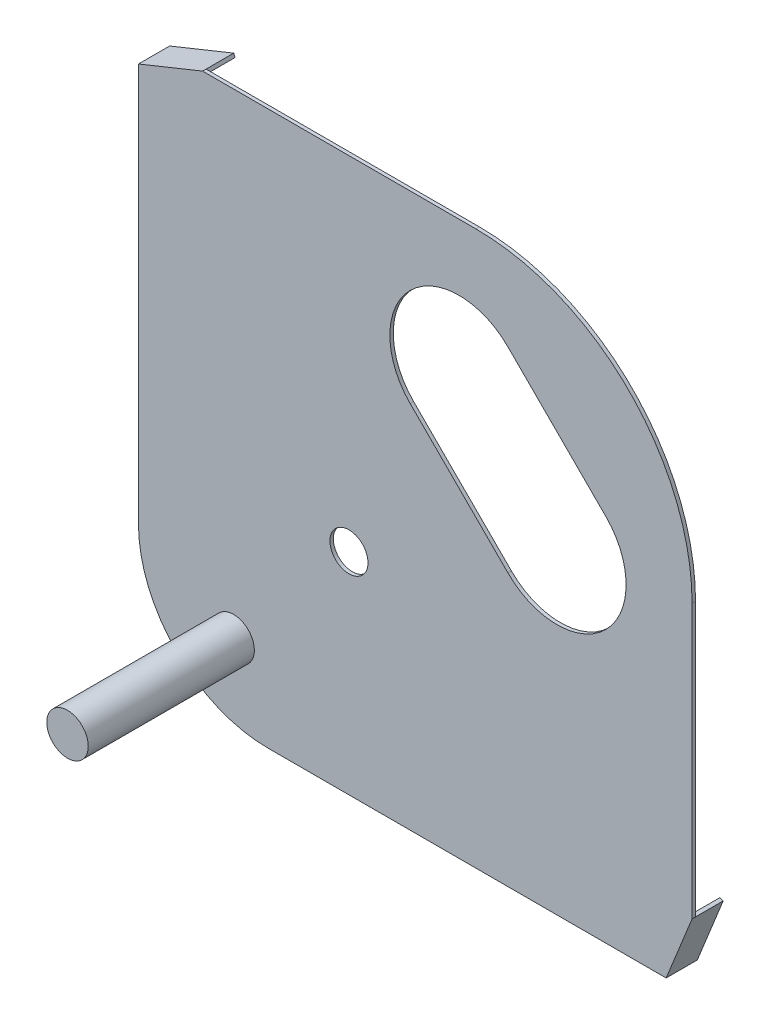
SolidWorks part; units mm, degrees
material "Nickel"
ref_plane "Front Plane" through (0, 0, 0) normal (0, 0, 1) x (1, 0, 0)
ref_plane "Top Plane" through (0, 0, 0) normal (0, 1, 0) x (1, 0, 0)
ref_plane "Right Plane" through (0, 0, 0) normal (1, 0, 0) x (0, 0, -1)
sketch "Sketch1" plane through (0, 0, 0) normal (0, 0, 1) x (1, 0, 0)
  line L0 (0, -9.525) -> (29.212, -9.525)
  line L1 (-9.525, 0) -> (-9.525, 29.212)
  line L2 (-4.8149, 31.115) -> (15.24, 31.115)
  line L3 (31.115, 15.24) -> (31.115, -4.8149)
  line L4 (31.115, -4.8149) -> (29.212, -9.525)
  line L5 (-9.525, 29.212) -> (-4.8149, 31.115)
  arc A0 (-9.525, 0) -> (0, -9.525) centre (0, 0) ccw
  arc A1 (31.115, 15.24) -> (15.24, 31.115) centre (15.24, 15.24) ccw
  dimension "D1" = 19.05
  dimension "D2" = 5.08
  dimension "D4" = 31.75
  dimension "D3" = 40.64
  dimension "D5" = 40.64
  dimension "D6" = 22
  dimension "D7" = 5.08
  dimension "D8" = 22
extrude "Boss-Extrude1" add sketch "Sketch1" against normal blind 0.254
sketch "Sketch2" plane through (0, 0, 0) normal (0, 0, 1) x (1, 0, 0)
  circle A0 centre (0, 0) radius 2.032
  dimension "D1" = 4.064
extrude "Cut-Extrude1" cut sketch "Sketch2" against normal blind 0.254
sketch "Sketch3" plane through (0, 0, 0) normal (0, 0, 1) x (1, 0, 0)
  line L0 (0, 0) -> (25.1279, 25.1279) construction
  line L1 (0, 0) -> (39.3207, 0) construction
  line L2 (0, -9.525) -> (29.212, -9.525) construction
  circle A0 centre (5.927, 5.927) radius 1.397
  dimension "D2" = 2.794
  dimension "D1" = 45
  dimension "D3" = 8.382
  dimension "D4" = 9.525
extrude "Cut-Extrude2" cut sketch "Sketch3" against normal blind 0.254
sketch "Sketch4" plane through (0, 0, 0) normal (0, 0, 1) x (1, 0, 0)
  line L0 (14.0092, 21.1934) -> (21.1934, 14.0092) construction
  line L1 (17.6013, 24.7855) -> (24.7855, 17.6013)
  line L2 (10.4171, 17.6013) -> (17.6013, 10.4171)
  line L3 (0, 0) -> (5.927, 5.927) construction
  line L4 (5.927, 5.927) -> (25.5434, 25.5434) construction
  arc A1 (17.6013, 24.7855) -> (10.4171, 17.6013) centre (14.0092, 21.1934) ccw
  arc A2 (17.6013, 10.4171) -> (24.7855, 17.6013) centre (21.1934, 14.0092) ccw
  point P2 (17.6013, 17.6013)
  dimension "D1" = 10.16
  dimension "D2" = 20.32
  dimension "D3" = 16.51
extrude "Cut-Extrude3" cut sketch "Sketch4" against normal blind 0.254 contours A2 L1 A1 L2
sketch "Sketch5" plane through (0, 0, 0) normal (0, 0, 1) x (1, 0, 0)
  line L0 (0, 0) -> (0, -6.3564)
  line L1 (0, 0) -> (-8.0615, 0)
  circle A0 centre (-2.54, -3.81) radius 1.524
  dimension "D1" = 3.048
  dimension "D2" = 3.81
  dimension "D3" = 2.54
sketch "Sketch6" plane through (0, 0, 0) normal (0, 0, 1) x (1, 0, 0)
extrude "Boss-Extrude2" add sketch "Sketch5" along normal blind 12.192 contours A0
sketch "Sketch7" plane through (0, 0, 0) normal (0, 0, 1) x (1, 0, 0)
  line L0 (0, 0) -> (28.6205, 0) construction
  line L1 (0, 0) -> (28.3973, 28.3973) construction
  line L2 (27.8877, 24.8344) -> (27.7081, 24.6548)
  line L3 (27.7081, 24.6548) -> (24.6548, 27.7081)
  line L4 (24.6548, 27.7081) -> (24.8344, 27.8877)
  line L5 (-9.4298, 28.9765) -> (-4.7198, 30.8795)
  line L6 (-4.8149, 31.115) -> (-4.7198, 30.8795)
  line L7 (-9.525, 29.212) -> (-9.4298, 28.9765)
  line L8 (29.212, -9.525) -> (31.115, -4.8149)
  line L9 (0, -9.525) -> (29.212, -9.525)
  line L10 (-9.525, 29.212) -> (-9.525, 0)
  line L11 (-4.8149, 31.115) -> (-9.525, 29.212)
  line L12 (15.24, 31.115) -> (-4.8149, 31.115)
  line L13 (31.115, -4.8149) -> (31.115, 15.24)
  line L14 (29.212, -9.525) -> (31.115, -4.8149)
  line L15 (0, -9.525) -> (29.212, -9.525)
  line L16 (-9.525, 29.212) -> (-9.525, 0)
  line L17 (-4.8149, 31.115) -> (-9.525, 29.212)
  line L18 (15.24, 31.115) -> (-4.8149, 31.115)
  line L19 (31.115, -4.8149) -> (31.115, 15.24)
  line L20 (28.9765, -9.4298) -> (30.8795, -4.7198)
  line L21 (31.115, -4.8149) -> (30.8795, -4.7198)
  line L22 (29.212, -9.525) -> (28.9765, -9.4298)
  arc A2 (-9.525, 0) -> (0, -9.525) centre (0, 0) ccw
  arc A3 (31.115, 15.24) -> (15.24, 31.115) centre (15.24, 15.24) ccw
  arc A4 (-9.525, 0) -> (0, -9.525) centre (0, 0) ccw
  arc A5 (31.115, 15.24) -> (15.24, 31.115) centre (15.24, 15.24) ccw
  point P13 (26.1814, 26.1814)
  line M10 (29.212, -9.525) -> (31.115, -4.8149)
  arc M12 (31.115, 15.24) -> (15.24, 31.115) centre (15.24, 15.24) ccw
  line M14 (-4.8149, 31.115) -> (-9.525, 29.212)
  dimension "D1" = 45
  dimension "D3" = 0.254
  dimension "D4" = 4.318
  dimension "D5" = 0.254
  dimension "D6" = 0.254
  dimension "D2" = 0
extrude "Boss-Extrude3" add sketch "Sketch7" against normal blind 2.286 contours L22 L21 L20 M10 | L4 L3 L2 M12 | L7 L5 L6 M14
sketch "Sketch8" plane through (0, 0, 0) normal (0, 0, 1) x (1, 0, 0)
  circle A0 centre (0, 0) radius 2.0518
extrude "Boss-Extrude4" add sketch "Sketch8" against normal blind 0.254
sketch "Sketch9" plane through (-1.5266, 1.5266, 0) normal (-0.7071, 0.7071, 0) x (0, 0, 1)
  line L1 (-0.254, 37.0261) -> (-2.8399, 37.0261)
  line L2 (-0.254, 37.0261) -> (-0.254, 37.6979)
  line L3 (-0.254, 37.6979) -> (-2.8399, 37.6979)
  line L4 (-2.8399, 37.0261) -> (-2.8399, 37.6979)
extrude "Cut-Extrude4" cut sketch "Sketch9" against normal through all
